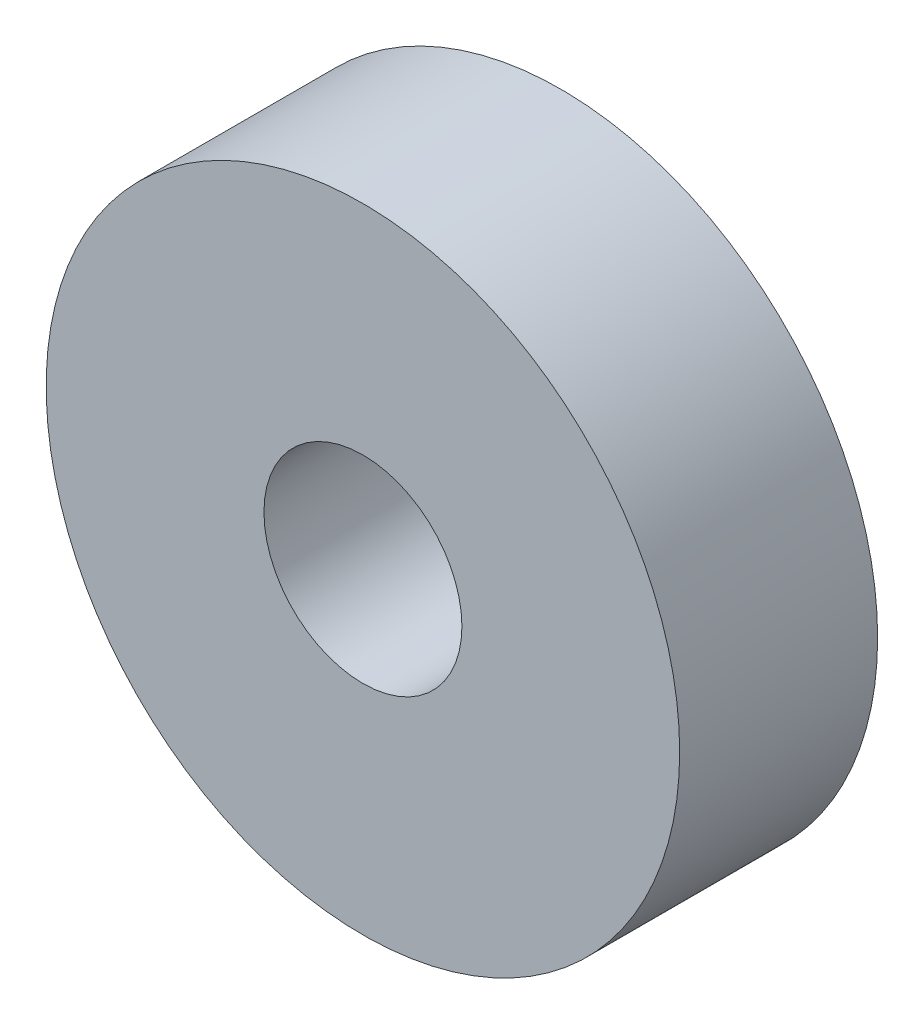
SolidWorks part; units mm, degrees
ref_plane "Alzado" through (0, 0, 0) normal (0, 0, 1) x (1, 0, 0)
ref_plane "Planta" through (0, 0, 0) normal (0, 1, 0) x (1, 0, 0)
ref_plane "Vista lateral" through (0, 0, 0) normal (1, 0, 0) x (0, 0, -1)
sketch "Croquis1" plane through (0, 0, 0) normal (0, 0, 1) x (1, 0, 0)
  circle A0 centre (0, 0) radius 2.5
  circle A1 centre (0, 0) radius 8
  dimension "D1" = 5
  dimension "D2" = 16
extrude "Saliente-Extruir1" add sketch "Croquis1" along normal blind 5
